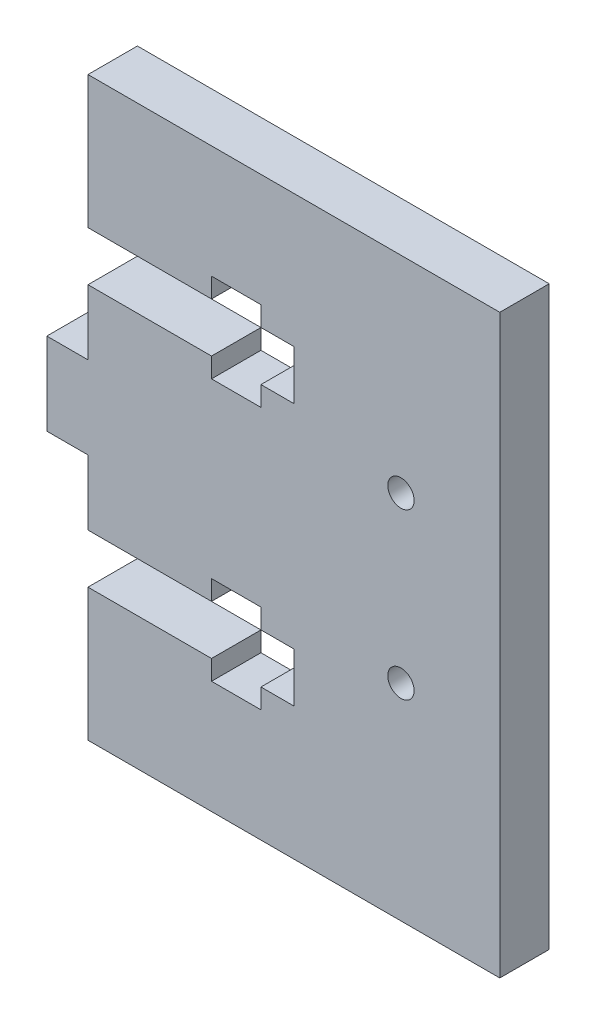
SolidWorks part; units mm, degrees
ref_plane "Front Plane" through (0, 0, 0) normal (0, 0, 1) x (1, 0, 0)
ref_plane "Top Plane" through (0, 0, 0) normal (0, 1, 0) x (1, 0, 0)
ref_plane "Right Plane" through (0, 0, 0) normal (1, 0, 0) x (0, 0, -1)
sketch "Sketch1" plane through (0, 0, 0) normal (0, 0, 1) x (1, 0, 0)
  line L0 (-100, 18.9) -> (-100, 21.3) construction
  line L1 (-71, -35) -> (-121, -35)
  line L2 (-71, -35) -> (-71, 35)
  line L3 (-71, 35) -> (-121, 35)
  line L4 (-121, -35) -> (-121, -18.9)
  line L5 (-71, -35) -> (-121, 35) construction
  line L6 (-71, 35) -> (-121, -35) construction
  line L7 (-96, 12.9) -> (-96, 18.9) construction
  line L8 (-100, 12.9) -> (-96, 12.9) construction
  line L9 (-100, 10.5) -> (-100, 12.9) construction
  line L10 (-106, 12.9) -> (-106, 10.5) construction
  line L11 (-106, 10.5) -> (-100, 10.5) construction
  line L12 (-121, 12.9) -> (-106, 12.9) construction
  line L13 (-106, 18.9) -> (-121, 18.9) construction
  line L14 (-106, 21.3) -> (-106, 18.9) construction
  line L15 (-100, 21.3) -> (-106, 21.3) construction
  line L16 (-96, 18.9) -> (-100, 18.9) construction
  line L17 (-100, 18.9) -> (-100, 21.3)
  line L18 (-96, 12.9) -> (-96, 18.9)
  line L19 (-100, 12.9) -> (-96, 12.9)
  line L20 (-100, 10.5) -> (-100, 12.9)
  line L21 (-106, 12.9) -> (-106, 10.5)
  line L22 (-106, 10.5) -> (-100, 10.5)
  line L23 (-121, 12.9) -> (-106, 12.9)
  line L24 (-106, 18.9) -> (-121, 18.9)
  line L25 (-106, 21.3) -> (-106, 18.9)
  line L26 (-100, 21.3) -> (-106, 21.3)
  line L27 (-96, 18.9) -> (-100, 18.9)
  line L28 (-121, 0) -> (-126, 0) construction
  line L29 (-121, 5) -> (-126, 5)
  line L30 (-121, -5) -> (-126, -5)
  line L31 (-126, 5) -> (-126, -5)
  line L32 (-121, 5) -> (-121, 12.9)
  line L38 (-100, -10.5) -> (-106, -10.5) construction
  line L39 (-100, -12.9) -> (-100, -10.5) construction
  line L40 (-96, -12.9) -> (-100, -12.9) construction
  line L41 (-106, -18.9) -> (-106, -21.3) construction
  line L42 (-96, -18.9) -> (-96, -12.9) construction
  line L43 (-100, -18.9) -> (-96, -18.9) construction
  line L44 (-100, -21.3) -> (-100, -18.9) construction
  line L45 (-106, -21.3) -> (-100, -21.3) construction
  line L46 (-121, -18.9) -> (-106, -18.9) construction
  line L47 (-106, -12.9) -> (-121, -12.9) construction
  line L48 (-106, -10.5) -> (-106, -12.9) construction
  line L49 (-106, -10.5) -> (-106, -12.9)
  line L50 (-100, -10.5) -> (-106, -10.5)
  line L51 (-100, -12.9) -> (-100, -10.5)
  line L52 (-96, -12.9) -> (-100, -12.9)
  line L53 (-106, -18.9) -> (-106, -21.3)
  line L54 (-96, -18.9) -> (-96, -12.9)
  line L55 (-100, -18.9) -> (-96, -18.9)
  line L56 (-100, -21.3) -> (-100, -18.9)
  line L57 (-106, -21.3) -> (-100, -21.3)
  line L58 (-121, -18.9) -> (-106, -18.9)
  line L59 (-106, -12.9) -> (-121, -12.9)
  line L60 (-121, -12.9) -> (-121, -5)
  line L61 (-121, 18.9) -> (-121, 35)
  circle A0 centre (-83, -10) radius 1.6 construction
  circle A1 centre (-83, 10) radius 1.6 construction
  circle A2 centre (-83, -10) radius 1.6
  circle A3 centre (-83, 10) radius 1.6
  point P0 (-96, 0)
  dimension "D1" = 50
  dimension "D2" = 5
  dimension "D3" = 5
  dimension "D4" = 5
extrude "Boss-Extrude1" add sketch "Sketch1" along normal blind 6 contours L2 L3 L61 L24 L25 L26 L17 L27 L18 L19 L20 L22 L21 L23 L60 L59 L49 L50 L51 L52 L54 L55 L56 L57 L53 L58 L4 L1
